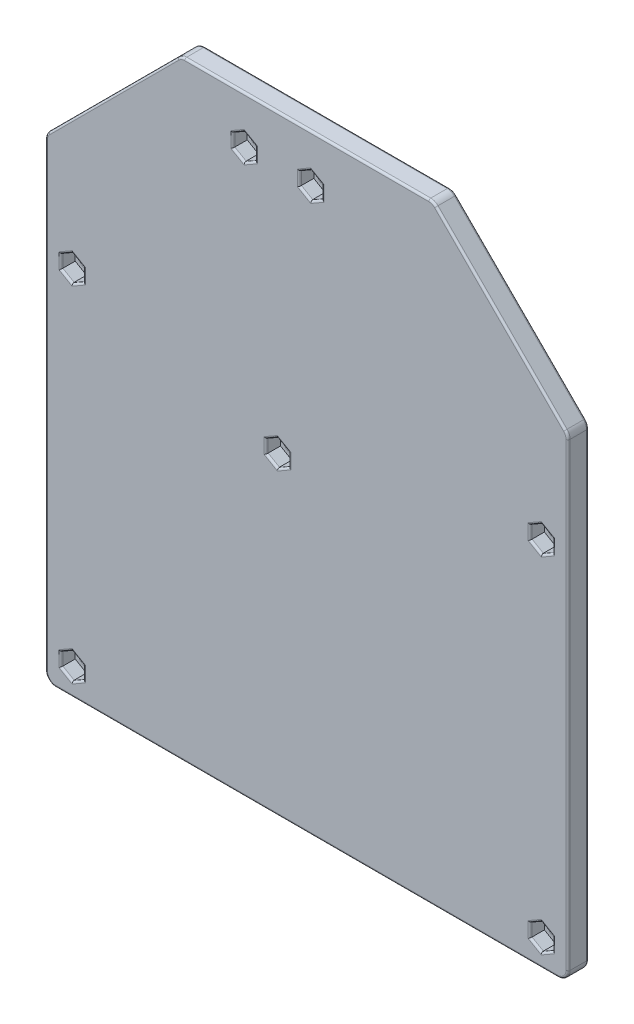
SolidWorks part; units mm, degrees
ref_plane "Front Plane" through (0, 0, 0) normal (0, 0, 1) x (1, 0, 0)
ref_plane "Top Plane" through (0, 0, 0) normal (0, 1, 0) x (1, 0, 0)
ref_plane "Right Plane" through (0, 0, 0) normal (1, 0, 0) x (0, 0, -1)
sketch "Sketch1" plane through (0, 0, 0) normal (0, 0, 1) x (1, 0, 0)
  line L0 (36.8145, -26.3) -> (-98.0645, -26.3) construction
  line L1 (-56.442, -174.5758) -> (70.7035, -174.5758)
  line L2 (-56.442, -174.5758) -> (-56.442, -26.3) construction
  line L3 (-56.442, -26.3) -> (70.7035, -26.3) construction
  line L4 (70.7035, -174.5758) -> (70.7035, -26.3) construction
  line L5 (64.2035, -174.5758) -> (-49.942, -174.5758) construction
  line L6 (-56.442, -26.3) -> (37.85, -26.3) construction
  line L7 (37.85, -26.3) -> (70.7035, -59.1535)
  line L8 (70.7035, -59.1535) -> (70.7035, -174.5758)
  line L9 (-56.442, -59.1535) -> (-23.5885, -26.3)
  line L10 (37.85, -26.3) -> (-23.5885, -26.3)
  line L11 (-56.442, -59.1535) -> (-56.442, -174.5758)
  circle A0 centre (-49.942, -168.0758) radius 1.5 construction
  circle A1 centre (64.2035, -168.0758) radius 1.5 construction
  circle A2 centre (-49.942, -84.2574) radius 1.5 construction
  circle A3 centre (64.2035, -84.2574) radius 1.5 construction
  circle A4 centre (0, -98.2299) radius 1.5 construction
  circle A5 centre (8.1, -37.8) radius 1.5 construction
  circle A6 centre (-8.1, -37.8) radius 1.5 construction
  circle A7 centre (-49.942, -168.0758) radius 1.5
  circle A8 centre (64.2035, -168.0758) radius 1.5
  circle A9 centre (-49.942, -84.2574) radius 1.5
  circle A10 centre (64.2035, -84.2574) radius 1.5
  circle A11 centre (0, -98.2299) radius 1.5
  circle A12 centre (8.1, -37.8) radius 1.5
  circle A13 centre (-8.1, -37.8) radius 1.5
  arc A14 (-49.942, -77.7574) -> (-49.942, -90.7574) centre (-49.942, -84.2574) ccw construction
  arc A15 (64.2035, -90.7574) -> (64.2035, -77.7574) centre (64.2035, -84.2574) ccw construction
  dimension "D1" = 45
  dimension "D2" = 45
extrude "Boss-Extrude1" add sketch "Sketch1" along normal blind 1.5
sketch "Sketch2" plane through (0, 0, 1.5) normal (0, 0, 1) x (1, 0, 0)
  line L0 (70.7035, -59.1535) -> (70.7035, -174.5758) construction
  line L1 (8.1, -34.6246) -> (5.35, -36.2123)
  line L2 (5.35, -36.2123) -> (5.35, -39.3877)
  line L3 (5.35, -39.3877) -> (8.1, -40.9754)
  line L4 (8.1, -40.9754) -> (10.85, -39.3877)
  line L5 (10.85, -39.3877) -> (10.85, -36.2123)
  line L6 (10.85, -36.2123) -> (8.1, -34.6246)
  line L7 (-8.1, -34.6246) -> (-10.85, -36.2123)
  line L8 (-10.85, -36.2123) -> (-10.85, -39.3877)
  line L9 (-10.85, -39.3877) -> (-8.1, -40.9754)
  line L10 (-8.1, -40.9754) -> (-5.35, -39.3877)
  line L11 (-5.35, -39.3877) -> (-5.35, -36.2123)
  line L12 (-5.35, -36.2123) -> (-8.1, -34.6246)
  line L13 (64.2035, -81.082) -> (61.4535, -82.6697)
  line L14 (61.4535, -82.6697) -> (61.4535, -85.8452)
  line L15 (61.4535, -85.8452) -> (64.2035, -87.4329)
  line L16 (64.2035, -87.4329) -> (66.9535, -85.8452)
  line L17 (66.9535, -85.8452) -> (66.9535, -82.6697)
  line L18 (66.9535, -82.6697) -> (64.2035, -81.082)
  line L19 (0, -95.0544) -> (-2.75, -96.6422)
  line L20 (-2.75, -96.6422) -> (-2.75, -99.8176)
  line L21 (-2.75, -99.8176) -> (0, -101.4053)
  line L22 (0, -101.4053) -> (2.75, -99.8176)
  line L23 (2.75, -99.8176) -> (2.75, -96.6422)
  line L24 (2.75, -96.6422) -> (0, -95.0544)
  line L25 (-49.942, -81.082) -> (-52.692, -82.6697)
  line L26 (-52.692, -82.6697) -> (-52.692, -85.8452)
  line L27 (-52.692, -85.8452) -> (-49.942, -87.4329)
  line L28 (-49.942, -87.4329) -> (-47.192, -85.8452)
  line L29 (-47.192, -85.8452) -> (-47.192, -82.6697)
  line L30 (-47.192, -82.6697) -> (-49.942, -81.082)
  line L31 (-49.942, -164.9004) -> (-52.692, -166.4881)
  line L32 (-52.692, -166.4881) -> (-52.692, -169.6635)
  line L33 (-52.692, -169.6635) -> (-49.942, -171.2512)
  line L34 (-49.942, -171.2512) -> (-47.192, -169.6635)
  line L35 (-47.192, -169.6635) -> (-47.192, -166.4881)
  line L36 (-47.192, -166.4881) -> (-49.942, -164.9004)
  line L37 (64.2035, -164.9004) -> (61.4535, -166.4881)
  line L38 (61.4535, -166.4881) -> (61.4535, -169.6635)
  line L39 (61.4535, -169.6635) -> (64.2035, -171.2512)
  line L40 (64.2035, -171.2512) -> (66.9535, -169.6635)
  line L41 (66.9535, -169.6635) -> (66.9535, -166.4881)
  line L42 (66.9535, -166.4881) -> (64.2035, -164.9004)
  line L43 (-56.442, -174.5758) -> (70.7035, -174.5758) construction
  line L46 (37.85, -26.3) -> (70.7035, -59.1535) construction
  line L47 (70.7035, -59.1535) -> (70.7035, -174.5758)
  line L48 (-56.442, -174.5758) -> (70.7035, -174.5758)
  line L51 (37.85, -26.3) -> (70.7035, -59.1535)
  line L52 (37.85, -26.3) -> (-23.5885, -26.3) construction
  line L53 (-56.442, -59.1535) -> (-23.5885, -26.3) construction
  line L54 (-56.442, -59.1535) -> (-56.442, -174.5758) construction
  line L55 (37.85, -26.3) -> (-23.5885, -26.3)
  line L56 (-56.442, -59.1535) -> (-23.5885, -26.3)
  line L57 (-56.442, -59.1535) -> (-56.442, -174.5758)
  circle A0 centre (8.1, -37.8) radius 2.75 construction
  circle A1 centre (-8.1, -37.8) radius 2.75 construction
  circle A2 centre (64.2035, -84.2574) radius 2.75 construction
  circle A3 centre (0, -98.2299) radius 2.75 construction
  circle A4 centre (-49.942, -84.2574) radius 2.75 construction
  circle A5 centre (-49.942, -168.0758) radius 2.75 construction
  circle A6 centre (64.2035, -168.0758) radius 2.75 construction
  dimension "D1" = 5.5
extrude "Boss-Extrude2" add sketch "Sketch2" along normal blind 3.5
fillet "Fillet1" radius 2.5 6 edges at (70.7035, -59.1535, 2.5) (70.7035, -174.5758, 2.5) (37.85, -26.3, 2.5) (-23.5885, -26.3, 2.5) (-56.442, -59.1535, 2.5) (-56.442, -174.5758, 2.5)
fillet "Fillet2" radius 0.5 80 edges at (-6.6, -37.8, 0) (1.5, -98.2299, 0) (-48.442, -84.2574, 0) (-48.442, -168.0758, 0) (7.1308, -174.5758, 0) (69.9713, -173.8436, 0) (70.7035, -116.1324, 0) (70.5132, -59.2323, 0) (54.2767, -42.7267, 0) (65.7035, -168.0758, 0) (65.7035, -84.2574, 0) (9.6, -37.8, 0) (62.8285, -165.6942, 5) (61.4535, -168.0758, 5) (62.8285, -170.4574, 5) (65.5785, -170.4574, 5) (66.9535, -168.0758, 5) (65.5785, -165.6942, 5) (-51.317, -81.8759, 5) (-52.692, -84.2574, 5) (-51.317, -86.639, 5) (-48.567, -86.639, 5) (-47.192, -84.2574, 5) (-48.567, -81.8759, 5) (62.8285, -81.8759, 5) (61.4535, -84.2574, 5) (62.8285, -86.639, 5) (65.5785, -86.639, 5) (66.9535, -84.2574, 5) (65.5785, -81.8759, 5) (6.725, -35.4184, 5) (5.35, -37.8, 5) (6.725, -40.1816, 5) (9.475, -40.1816, 5) (10.85, -37.8, 5) (9.475, -35.4184, 5) (69.9713, -173.8436, 5) (7.1308, -174.5758, 5) (54.2767, -42.7267, 5) (70.5132, -59.2323, 5) (70.7035, -116.1324, 5) (-9.475, -35.4184, 5) (-10.85, -37.8, 5) (-9.475, -40.1816, 5) (-6.725, -40.1816, 5) (-5.35, -37.8, 5) (-6.725, -35.4184, 5) (-1.375, -95.8483, 5) (-2.75, -98.2299, 5) (-1.375, -100.6114, 5) (1.375, -100.6114, 5) (2.75, -98.2299, 5) (1.375, -95.8483, 5) (-51.317, -165.6942, 5) (-52.692, -168.0758, 5) (-51.317, -170.4574, 5) (-48.567, -170.4574, 5) (-47.192, -168.0758, 5) (-48.567, -165.6942, 5) (-48.442, -168.0758, 1.5) (65.7035, -168.0758, 1.5) (-48.442, -84.2574, 1.5) (1.5, -98.2299, 1.5) (65.7035, -84.2574, 1.5) (9.6, -37.8, 1.5) (-6.6, -37.8, 1.5) (7.1308, -26.3, 0) (-40.0152, -42.7267, 0) (-56.442, -116.1324, 0) (-56.442, -116.1324, 5) (-40.0152, -42.7267, 5) (7.1308, -26.3, 5) (-23.5096, -26.4903, 0) (-56.2517, -59.2323, 0) (-55.7097, -173.8436, 0) (37.7712, -26.4903, 0) (-55.7097, -173.8436, 5) (-56.2517, -59.2323, 5) (-23.5096, -26.4903, 5) (37.7712, -26.4903, 5)
